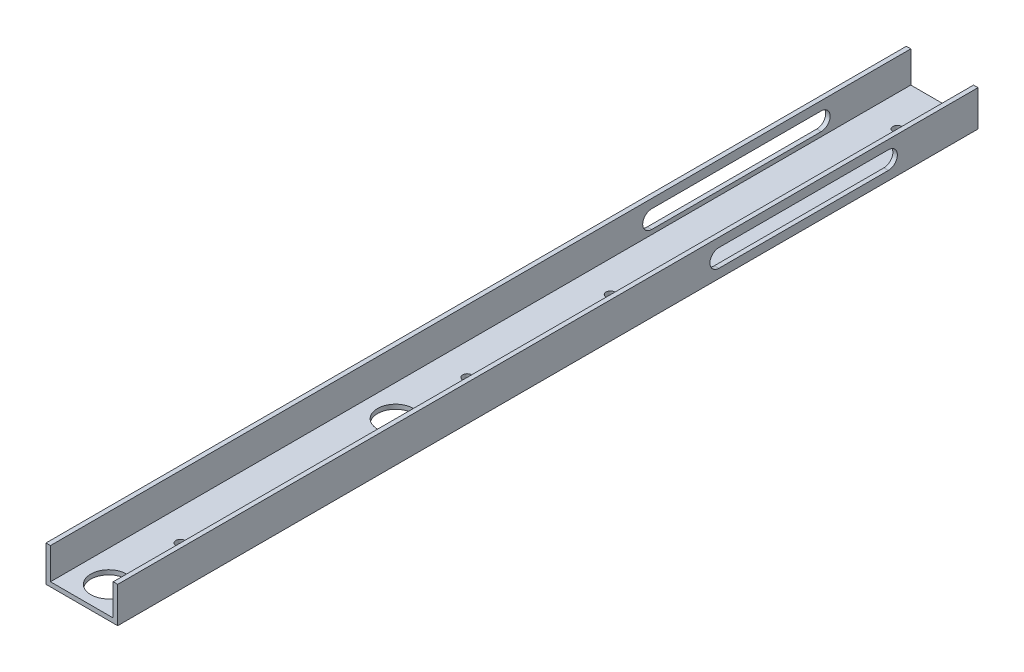
SolidWorks part; units mm, degrees
ref_plane "Front" through (0, 0, 0) normal (0, 0, 1) x (1, 0, 0)
ref_plane "Top" through (0, 0, 0) normal (0, 1, 0) x (1, 0, 0)
ref_plane "Right" through (0, 0, 0) normal (1, 0, 0) x (0, 0, -1)
sketch "Sketch1" plane through (0, 0, 0) normal (0, 0, 1) x (1, 0, 0)
  line L0 (47.625, 3.175) -> (47.625, 25.4)
  line L1 (0, 0) -> (50.8, 0)
  line L2 (0, 0) -> (0, 25.4)
  line L4 (50.8, 0) -> (50.8, 25.4)
  line L5 (3.175, 3.175) -> (47.625, 3.175)
  line L6 (3.175, 3.175) -> (3.175, 25.4)
  line L7 (50.8, 25.4) -> (47.625, 25.4)
  line L8 (0, 25.4) -> (3.175, 25.4)
  dimension "D1" = 25.4
  dimension "D2" = 50.8
  dimension "D3" = 3.175
extrude "Boss-Extrude1" add sketch "Sketch1" along normal blind 609.6
sketch "Sketch2" plane through (0, 3.175, 0) normal (0, 1, 0) x (1, 0, 0)
  line L0 (47.625, -609.6) -> (3.175, -609.6) construction
  circle A0 centre (25.4, -590.55) radius 12.7
  circle A1 centre (25.4, -387.35) radius 12.7
  circle A2 centre (25.4, -539.75) radius 3.175
  circle A3 centre (25.4, -336.55) radius 3.175
  dimension "D1" = 25.4
  dimension "D2" = 19.05
  dimension "D3" = 203.2
  dimension "D4" = 6.35
  dimension "D5" = 50.8
  dimension "D6" = 50.8
extrude "Cut-Extrude1" cut sketch "Sketch2" against normal up to next
sketch "Sketch3" plane through (0, 3.175, 0) normal (0, 1, 0) x (1, 0, 0)
  circle A0 centre (25.4, -234.95) radius 3.175
  circle A1 centre (25.4, -31.75) radius 3.175
  circle A2 centre (25.4, -387.35) radius 12.7 construction
  dimension "D1" = 6.35
  dimension "D2" = 203.2
  dimension "D3" = 152.4
extrude "Cut-Extrude2" cut sketch "Sketch3" against normal up to next
sketch "Sketch4" plane through (50.8, 0, 0) normal (1, 0, 0) x (0, 0, -1)
  line L0 (-63.5, 12.7) -> (-183.6067, 12.7) construction
  line L2 (-609.6, 25.4) -> (0, 25.4) construction
  line L3 (-183.6067, 12.7) -> (-63.5, 12.7) construction
  line L4 (-183.6067, 19.05) -> (-63.5, 19.05)
  line L5 (-183.6067, 6.35) -> (-63.5, 6.35)
  line L6 (0, 0) -> (0, 25.4) construction
  arc A0 (-183.6067, 19.05) -> (-183.6067, 6.35) centre (-183.6067, 12.7) ccw
  arc A1 (-63.5, 6.35) -> (-63.5, 19.05) centre (-63.5, 12.7) ccw
  point P2 (-123.5534, 12.7)
  dimension "D1" = 12.7
  dimension "D2" = 12.7
  dimension "D3" = 183.6067
  dimension "D4" = 63.5
extrude "Cut-Extrude3" cut sketch "Sketch4" against normal through all
